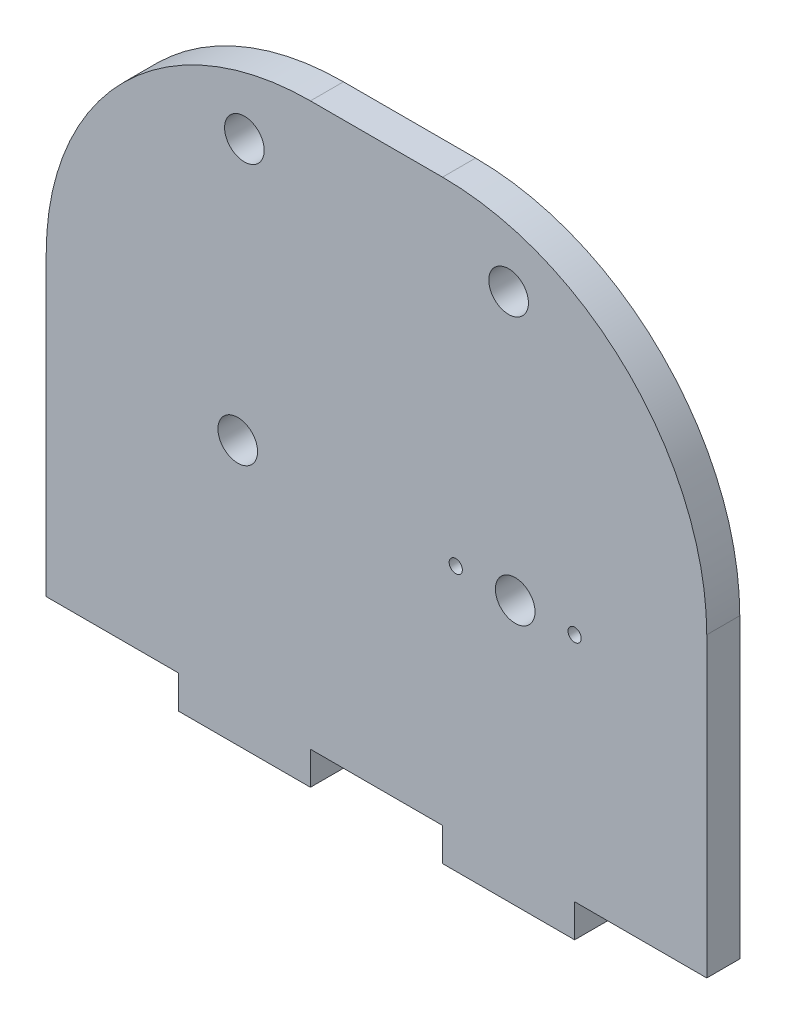
SolidWorks part; units mm, degrees
ref_plane "Alzado" through (0, 0, 0) normal (0, 0, 1) x (1, 0, 0)
ref_plane "Planta" through (0, 0, 0) normal (0, 1, 0) x (1, 0, 0)
ref_plane "Vista lateral" through (0, 0, 0) normal (1, 0, 0) x (0, 0, -1)
sketch "Croquis1" plane through (0, 0, 0) normal (0, 0, 1) x (1, 0, 0)
  line L0 (15, -10) -> (10.5, -10) construction
  line L2 (-25, -15) -> (-25, -5)
  line L3 (-5, 15) -> (5, 15)
  line L4 (25, -15) -> (25, -5)
  line L5 (-25, -15) -> (25, 15) construction
  line L6 (-25, 15) -> (25, -15) construction
  line L7 (10.5, -10) -> (6, -10) construction
  line L9 (10, 10) -> (-10, 10) construction
  line L10 (-25, -15) -> (-25, -27.5)
  line L11 (-25, -27.5) -> (-15, -27.5)
  line L12 (25, -15) -> (25, -27.5)
  line L13 (-15, -27.5) -> (-15, -30)
  line L14 (-15, -30) -> (-5, -30)
  line L15 (15, -30) -> (15, -27.5)
  line L16 (15, -27.5) -> (25, -27.5)
  line L17 (-5, -30) -> (-5, -27.5)
  line L18 (-5, -27.5) -> (5, -27.5)
  line L19 (5, -27.5) -> (5, -30)
  line L20 (5, -30) -> (15, -30)
  circle A0 centre (-10, 10) radius 1.5
  circle A1 centre (10, 10) radius 1.5
  arc A2 (-25, -5) -> (-5, 15) centre (-5, -5) cw
  arc A3 (25, -5) -> (5, 15) centre (5, -5) ccw
  circle A4 centre (-10.5, -10) radius 1.5
  circle A5 centre (10.5, -10) radius 1.5
  circle A6 centre (15, -10) radius 0.5
  circle A7 centre (6, -10) radius 0.5
  point P0 (0, 0)
  point P6 (0, 0)
  dimension "D5" = 20
  dimension "D6" = 20
  dimension "D3" = 20
  dimension "D10" = 15
  dimension "D11" = 10
  dimension "D9" = 12.5
  dimension "D1" = 50
  dimension "D2" = 30
  dimension "D4" = 5
  dimension "D7" = 21
  dimension "D8" = 14.5
extrude "Saliente-Extruir1" add sketch "Croquis1" along normal blind 2.5
